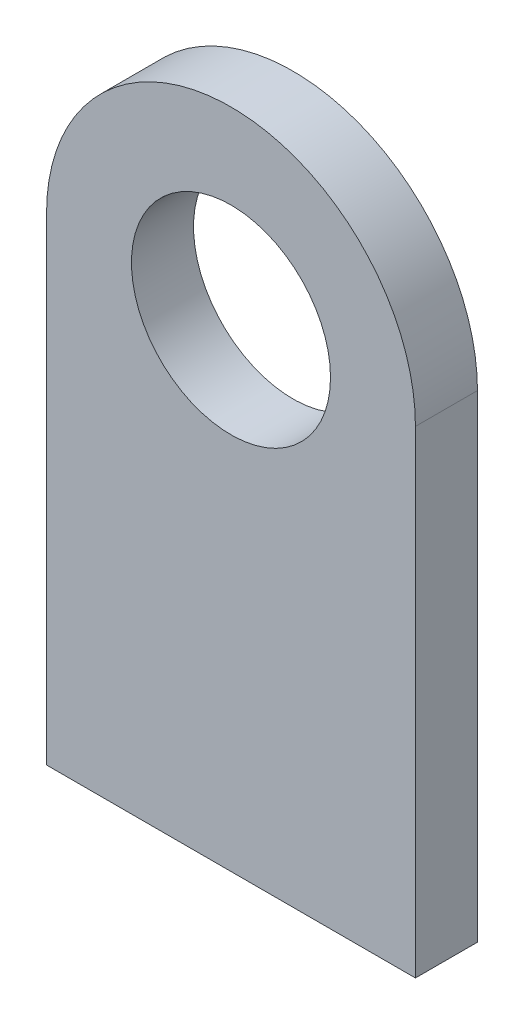
SolidWorks part; units mm, degrees
ref_plane "Front Plane" through (0, 0, 0) normal (0, 0, 1) x (1, 0, 0)
ref_plane "Top Plane" through (0, 0, 0) normal (0, 1, 0) x (1, 0, 0)
ref_plane "Right Plane" through (0, 0, 0) normal (1, 0, 0) x (0, 0, -1)
sketch "Sketch1" plane through (0, 0, 0) normal (0, 0, 1) x (1, 0, 0)
  line L2 (-27.8, 0) -> (-27.8, -72)
  line L3 (-27.8, -72) -> (27.8, -72)
  line L4 (27.8, 0) -> (27.8, -72)
  circle A0 centre (0, 0) radius 15
  arc A1 (27.8, 0) -> (-27.8, 0) centre (0, 0) ccw
  dimension "D1" = 30
  dimension "D2" = 55.6
  dimension "D3" = 72
extrude "Boss-Extrude1" add sketch "Sketch1" along normal blind 9.35
